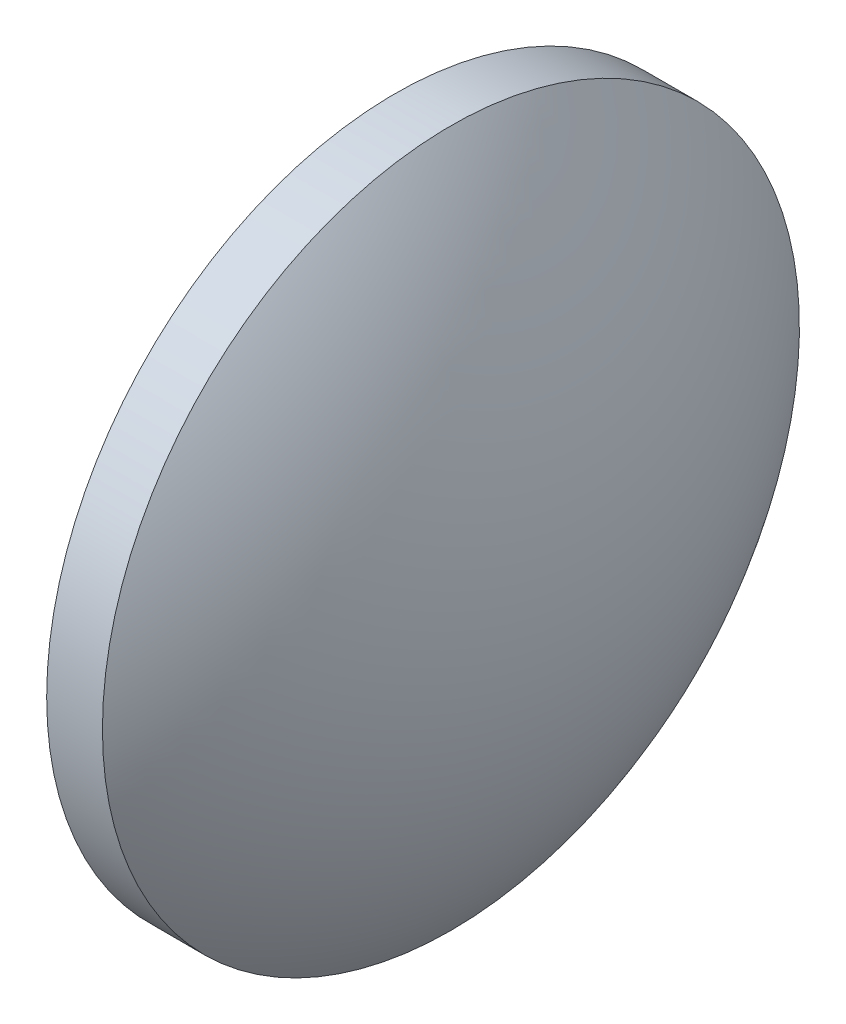
SolidWorks part; units mm, degrees
ref_plane "前视基准面" through (0, 0, 0) normal (0, 0, 1) x (1, 0, 0)
ref_plane "上视基准面" through (0, 0, 0) normal (0, 1, 0) x (1, 0, 0)
ref_plane "右视基准面" through (0, 0, 0) normal (1, 0, 0) x (0, 0, -1)
sketch "草图1" plane through (0, 0, 0) normal (0, 0, 1) x (1, 0, 0)
  line L0 (632.6575, 47.9466) -> (648.7145, 47.9466) construction
  line L1 (634.6866, 47.9466) -> (634.6866, 60.4466)
  line L2 (640.8966, 47.9466) -> (634.6866, 47.9466)
  line L5 (634.6866, 60.4466) -> (636.6866, 60.4466)
  arc A0 (640.8966, 47.9466) -> (636.6866, 60.4466) centre (620.2346, 47.9466) ccw
revolve "旋转1" add sketch "草图1" angle 360 about L0
